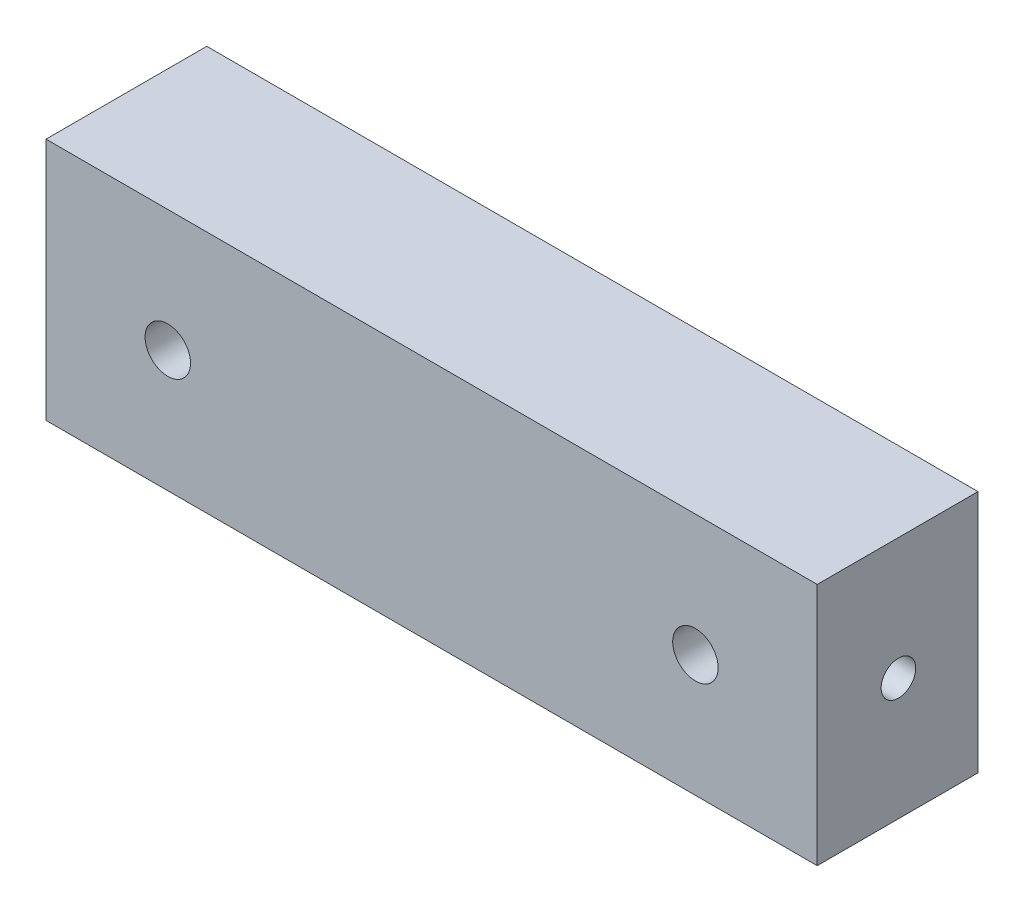
SolidWorks part; units mm, degrees
ref_plane "Front Plane" through (0, 0, 0) normal (0, 0, 1) x (1, 0, 0)
ref_plane "Top Plane" through (0, 0, 0) normal (0, 1, 0) x (1, 0, 0)
ref_plane "Right Plane" through (0, 0, 0) normal (1, 0, 0) x (0, 0, -1)
sketch "Sketch1" plane through (0, 0, 0) normal (0, 0, 1) x (1, 0, 0)
  line L1 (0, 0) -> (60.3123, 0)
  line L2 (0, 0) -> (0, 19.05)
  line L3 (0, 19.05) -> (60.3123, 19.05)
  line L4 (60.3123, 0) -> (60.3123, 19.05)
  dimension "D1" = 19.05
  dimension "D2" = 60.3123
extrude "Extrude1" add sketch "Sketch1" along normal blind 12.573
sketch "Sketch2" plane through (0, 0, 12.573) normal (0, 0, 1) x (1, 0, 0)
  line L0 (60.3123, 19.05) -> (0, 19.05) construction
  line L1 (60.3123, 0) -> (60.3123, 19.05) construction
  line L2 (0, 19.05) -> (0, 0) construction
  circle A0 centre (9.525, 9.525) radius 1.778
  circle A1 centre (50.7873, 9.525) radius 1.778
  dimension "D1" = 3.556
  dimension "D3" = 9.525
  dimension "D4" = 9.525
  dimension "D2" = 9.525
extrude "Cut-Extrude1" cut sketch "Sketch2" against normal through all
hole_wizard "#6-32 Tapped Hole1" positions "Sketch4" profile "Sketch3" tap size "#6-32" standard "Ansi Inch"
sketch "Sketch4" plane through (0, 0, 0) normal (-1, 0, 0) x (0, 0, 1)
  line L0 (12.573, 19.05) -> (0, 19.05) construction
  line L2 (12.573, 19.05) -> (12.573, 0) construction
  point P0 (6.223, 9.525)
  dimension "D1" = 9.525
  dimension "D2" = 6.35
sketch "Sketch3" plane through (0, 9.525, 6.223) normal (0, 1, 0) x (0, 0, 1)
  line L0 (0, 0) -> (0, 10.3377)
  line L1 (0, 10.3377) -> (1.3525, 9.525)
  line L2 (1.3525, 9.525) -> (1.3525, 0)
  line L5 (1.3525, 0) -> (0, 0)
  line L10 (0, 10.3377) -> (-1.3526, 9.525) construction
  line L11 (0, -6.35) -> (0, 107.95) construction
  dimension "Tap Drill Dia." = 2.7051
  dimension "Tap Drill Depth" = 9.525
  dimension "Drill Angle" = 118
cosmetic thread "Hole Thread1" parameters "D1"=7.0104, "D2"=3.5052
hole_wizard "#6-32 Tapped Hole2" positions "Sketch6" profile "Sketch5" tap size "#6-32" standard "Ansi Inch"
sketch "Sketch6" plane through (60.3123, 0, 0) normal (1, 0, 0) x (0, 0, -1)
  line L0 (-12.573, 19.05) -> (0, 19.05) construction
  line L1 (-12.573, 0) -> (-12.573, 19.05) construction
  point P0 (-6.223, 9.525)
  dimension "D1" = 9.525
  dimension "D2" = 6.35
sketch "Sketch5" plane through (60.3123, 9.525, 6.223) normal (0, 1, 0) x (0, 0, -1)
  line L0 (0, 0) -> (0, 10.3377)
  line L1 (0, 10.3377) -> (1.3525, 9.525)
  line L2 (1.3525, 9.525) -> (1.3525, 0)
  line L5 (1.3525, 0) -> (0, 0)
  line L10 (0, 10.3377) -> (-1.3525, 9.525) construction
  line L11 (0, -6.35) -> (0, 107.95) construction
  dimension "Tap Drill Dia." = 2.7051
  dimension "Tap Drill Depth" = 9.525
  dimension "Drill Angle" = 118
cosmetic thread "Hole Thread2" parameters "D1"=7.0104, "D2"=3.5052
